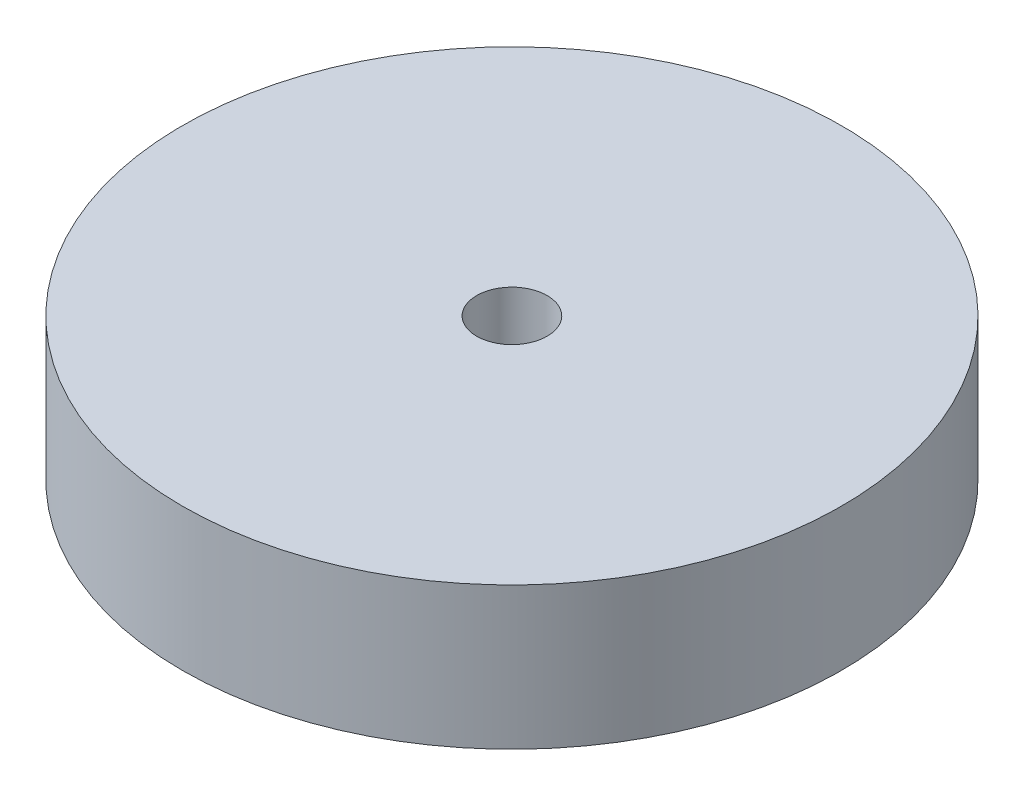
SolidWorks part; units mm, degrees
ref_plane "Front Plane" through (0, 0, 0) normal (0, 0, 1) x (1, 0, 0)
ref_plane "Top Plane" through (0, 0, 0) normal (0, 1, 0) x (1, 0, 0)
ref_plane "Right Plane" through (0, 0, 0) normal (1, 0, 0) x (0, 0, -1)
sketch "Sketch2" plane through (0, 0, 0) normal (0, 1, 0) x (1, 0, 0)
  circle A0 centre (0, 0) radius 200
  circle A1 centre (0, 0) radius 21.39
  dimension "D1" = 400
  dimension "D2" = 42.78
extrude "Boss-Extrude1" add sketch "Sketch2" along normal blind 86.36
